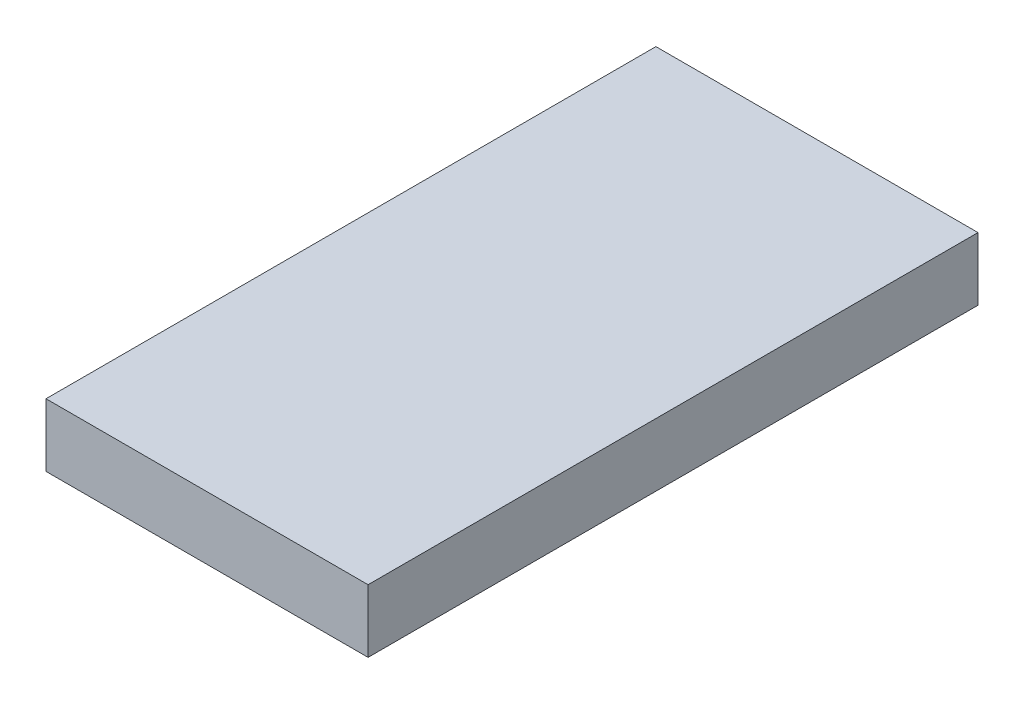
SolidWorks part; units mm, degrees
ref_plane "Front Plane" through (0, 0, 0) normal (0, 0, 1) x (1, 0, 0)
ref_plane "Top Plane" through (0, 0, 0) normal (0, 1, 0) x (1, 0, 0)
ref_plane "Right Plane" through (0, 0, 0) normal (1, 0, 0) x (0, 0, -1)
sketch "Sketch1" plane through (0, 0, 0) normal (0, 1, 0) x (1, 0, 0)
  line L1 (-17.907, -33.909) -> (17.907, -33.909)
  line L2 (-17.907, -33.909) -> (-17.907, 33.909)
  line L3 (-17.907, 33.909) -> (17.907, 33.909)
  line L4 (17.907, -33.909) -> (17.907, 33.909)
  line L5 (-17.907, -33.909) -> (17.907, 33.909) construction
  line L6 (-17.907, 33.909) -> (17.907, -33.909) construction
  point P0 (0, 0)
  dimension "D1" = 35.814
  dimension "D2" = 67.818
extrude "Boss-Extrude1" add sketch "Sketch1" along normal blind 7
